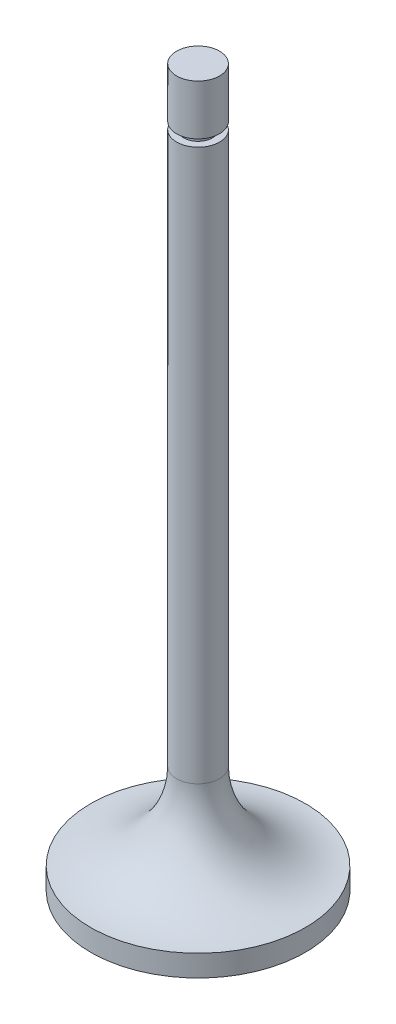
SolidWorks part; units mm, degrees
ref_plane "Front Plane" through (0, 0, 0) normal (0, 0, 1) x (1, 0, 0)
ref_plane "Top Plane" through (0, 0, 0) normal (0, 1, 0) x (1, 0, 0)
ref_plane "Right Plane" through (0, 0, 0) normal (1, 0, 0) x (0, 0, -1)
sketch "Sketch3" plane through (0, 0, 0) normal (0, 0, 1) x (1, 0, 0)
  line L0 (0, 0) -> (0, 22.8954)
  line L1 (0, 22.8954) -> (0, -77.1046)
  line L2 (0, -77.1046) -> (15, -77.1046)
  line L3 (15, -77.1046) -> (15, -74.1046)
  line L4 (0, 22.8954) -> (3, 22.8954)
  line L6 (0, 0) -> (0, 103.6492) construction
  line L11 (0, 103.6492) -> (0, -117.6934) construction
  line L13 (3, 22.8954) -> (3, -62.1046)
  line L14 (3, 15.8954) -> (2, 15.8954)
  line L15 (3, 15.8954) -> (3, 14.8954)
  line L16 (3, 14.8954) -> (2, 14.8954)
  line L17 (2, 15.8954) -> (2, 14.8954)
  arc A1 (3, -62.1046) -> (15, -74.1046) centre (15, -62.1046) ccw
  dimension "D1" = 100
  dimension "D2" = 15
  dimension "D3" = 3
  dimension "D4" = 3
  dimension "D5" = 85
  dimension "D6" = 1
  dimension "D7" = 1
  dimension "D8" = 7
revolve "Revolve1" add sketch "Sketch3" angle 360 about L11
